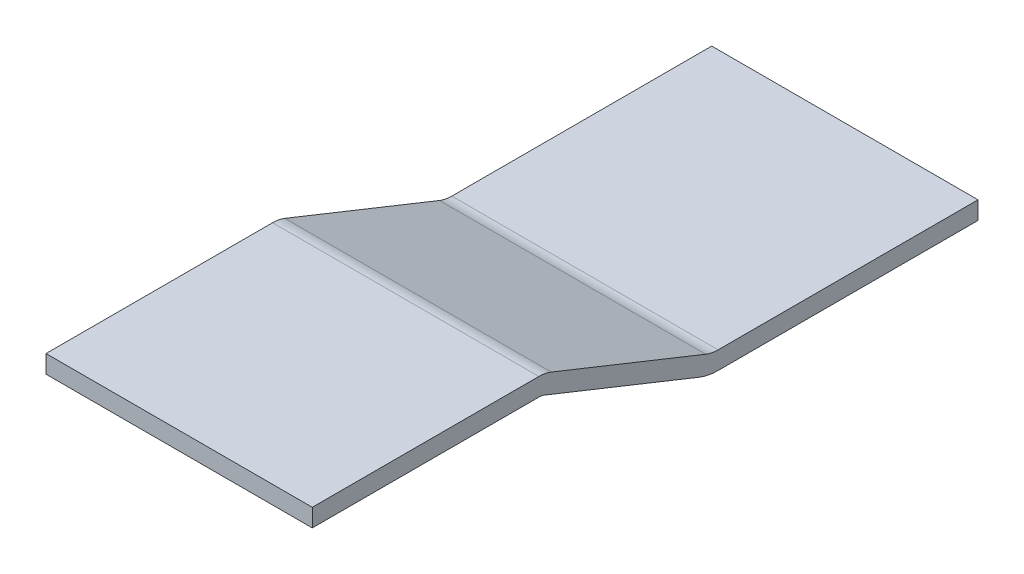
SolidWorks part; units mm, degrees
material "Plain Carbon Steel"
ref_plane "Front Plane" through (0, 0, 0) normal (0, 0, 1) x (1, 0, 0)
ref_plane "Top Plane" through (0, 0, 0) normal (0, 1, 0) x (1, 0, 0)
ref_plane "Right Plane" through (0, 0, 0) normal (1, 0, 0) x (0, 0, -1)
sketch "Sketch1" plane through (0, 0, 0) normal (1, 0, 0) x (0, 0, -1)
  line L0 (-21.6136, 0) -> (21.6136, 0)
  line L1 (23.9719, -0.4542) -> (53.451, -12.2458)
  line L2 (55.8093, -12.7) -> (105.3864, -12.7)
  line L3 (0, 22.6605) -> (0, -22.6605) construction
  arc A0 (53.451, -12.2458) -> (55.8093, -12.7) centre (55.8093, -6.35) ccw
  arc A1 (21.6136, 0) -> (23.9719, -0.4542) centre (21.6136, -6.35) cw
  point P7 (0, 0)
  point P8 (0, 0)
  point P11 (54.5864, -12.7)
  point P14 (22.8364, 0)
  dimension "D5" = 6.35
  dimension "D1" = 12.7
  dimension "D2" = 44.45
  dimension "D3" = 50.8
  dimension "D4" = 127
extrude "Base Thin" add sketch "Sketch1" along normal mid plane 50.8 thin
